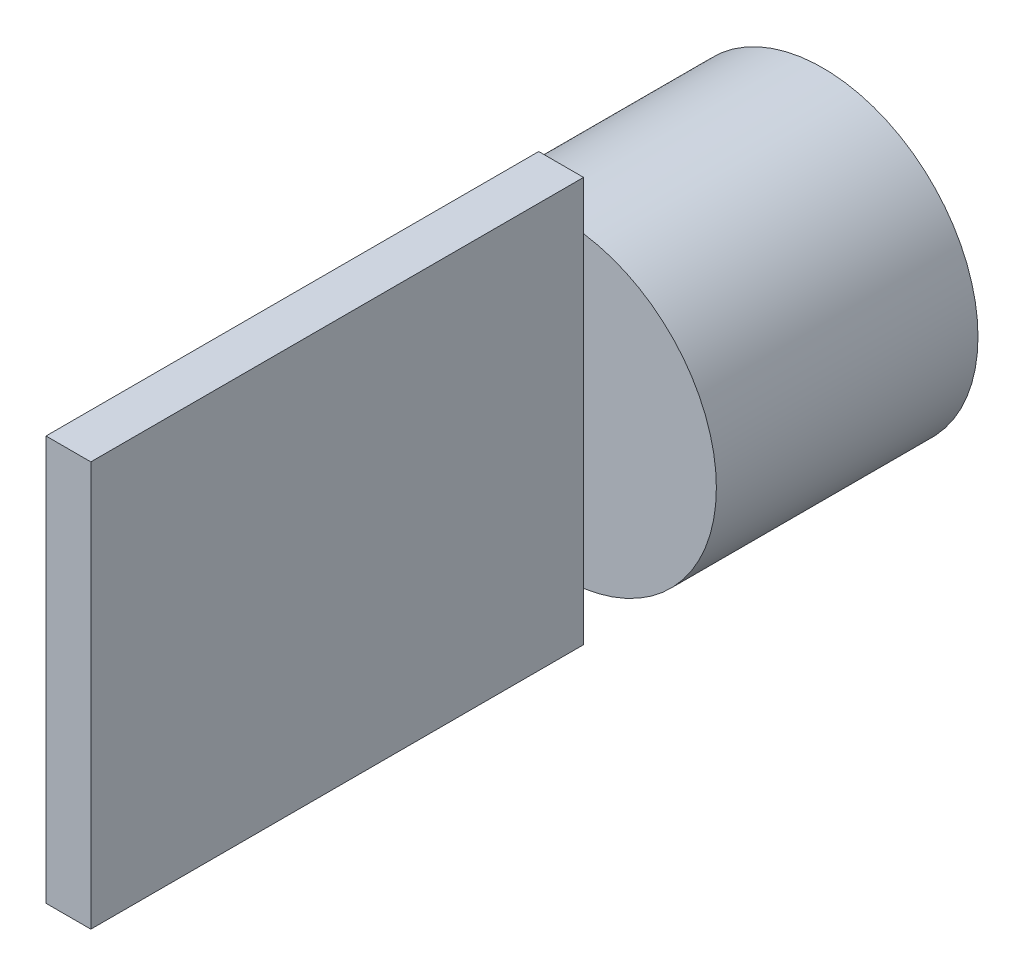
SolidWorks part; units mm, degrees
ref_plane "Ebene vorne" through (0, 0, 0) normal (0, 0, 1) x (1, 0, 0)
ref_plane "Ebene oben" through (0, 0, 0) normal (0, 1, 0) x (1, 0, 0)
ref_plane "Ebene rechts" through (0, 0, 0) normal (1, 0, 0) x (0, 0, -1)
sketch "Skizze1" plane through (0, 0, 0) normal (0, 0, 1) x (1, 0, 0)
  circle A0 centre (0, 0) radius 35.6
  dimension "D1" = 71.2
extrude "Aufsatz-Linear austragen1" add sketch "Skizze1" along normal blind 60
sketch "Skizze2" plane through (0, 0, 60) normal (0, 0, 1) x (1, 0, 0)
  line L1 (5.1416, 46.4093) -> (-5.1416, 46.4093)
  line L2 (5.1416, 46.4093) -> (5.1416, -46.4093)
  line L3 (5.1416, -46.4093) -> (-5.1416, -46.4093)
  line L4 (-5.1416, 46.4093) -> (-5.1416, -46.4093)
  line L5 (5.1416, 46.4093) -> (-5.1416, -46.4093) construction
  line L6 (5.1416, -46.4093) -> (-5.1416, 46.4093) construction
  point P0 (0, 0)
extrude "Aufsatz-Linear austragen2" add sketch "Skizze2" along normal blind 113
